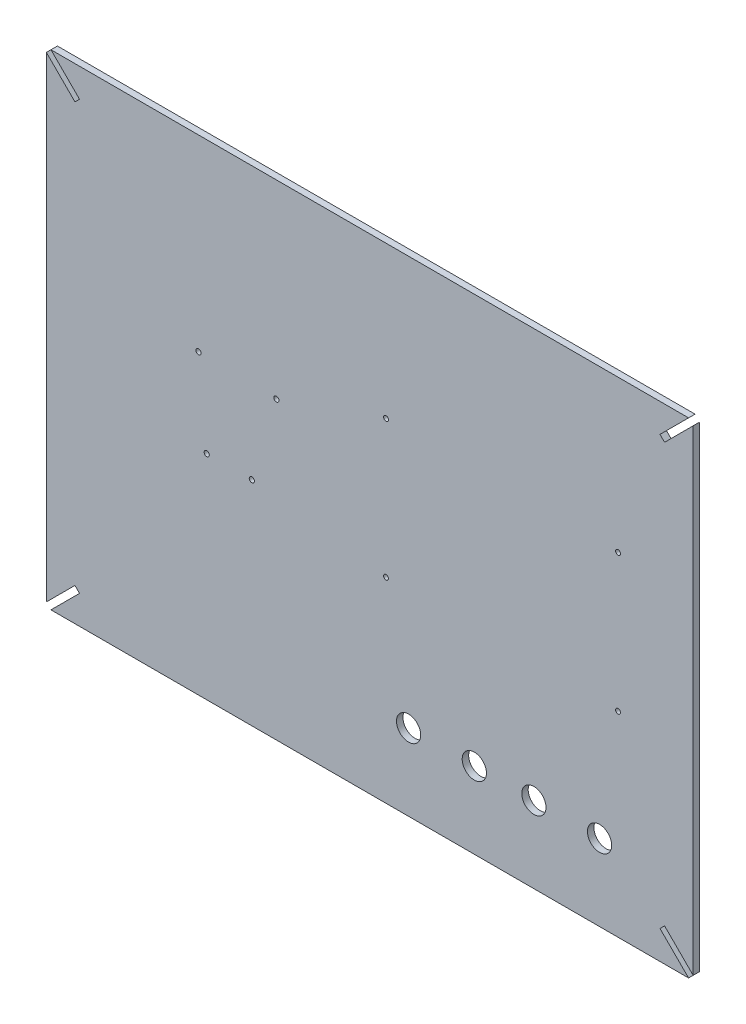
SolidWorks part; units mm, degrees
ref_plane "Plan de face" through (0, 0, 0) normal (0, 0, 1) x (1, 0, 0)
ref_plane "Plan de dessus" through (0, 0, 0) normal (0, 1, 0) x (1, 0, 0)
ref_plane "Plan de droite" through (0, 0, 0) normal (1, 0, 0) x (0, 0, -1)
sketch "Esquisse1" plane through (0, 0, 0) normal (0, 0, 1) x (1, 0, 0)
  line L0 (-443.8564, 119.1502) -> (-49.5132, 119.1502)
  line L1 (-446.6848, 119.1502) -> (-46.6848, 119.1502) construction
  line L2 (-446.6848, 119.1502) -> (-446.6848, -180.8498) construction
  line L3 (-446.6848, -180.8498) -> (-46.6848, -180.8498) construction
  line L4 (-46.6848, 119.1502) -> (-46.6848, -180.8498) construction
  line L5 (-446.6848, 116.3218) -> (-446.6848, -178.0213)
  line L6 (-443.8564, -180.8498) -> (-49.5132, -180.8498)
  line L7 (-46.6848, -178.0213) -> (-46.6848, 116.3218)
  line L8 (-46.6848, 116.3218) -> (-64.3625, 98.6441)
  line L9 (-64.3625, 98.6441) -> (-67.1909, 101.4726)
  line L10 (-67.1909, 101.4726) -> (-49.5132, 119.1502)
  line L11 (-46.6848, -178.0213) -> (-64.3625, -160.3437)
  line L12 (-64.3625, -160.3437) -> (-67.1909, -163.1721)
  line L13 (-67.1909, -163.1721) -> (-49.5132, -180.8498)
  line L14 (-443.8564, -180.8498) -> (-426.1787, -163.1721)
  line L15 (-426.1787, -163.1721) -> (-429.0071, -160.3437)
  line L16 (-429.0071, -160.3437) -> (-446.6848, -178.0213)
  line L17 (-443.8564, 119.1502) -> (-426.1787, 101.4726)
  line L18 (-426.1787, 101.4726) -> (-429.0071, 98.6441)
  line L19 (-429.0071, 98.6441) -> (-446.6848, 116.3218)
  line L20 (-60.4528, -17.2498) -> (-387.6528, -17.2498) construction
  line L21 (-410.2848, 82.7502) -> (-83.0848, 82.7502) construction
  line L22 (-410.2848, 82.7502) -> (-410.2848, -144.4498) construction
  line L23 (-410.2848, -144.4498) -> (-83.0848, -144.4498) construction
  line L24 (-83.0848, 82.7502) -> (-83.0848, -144.4498) construction
  line L25 (-240.4498, 29.1052) -> (-89.3198, 29.1052) construction
  line L26 (-240.4498, 29.1052) -> (-240.4498, -63.6048) construction
  line L27 (-240.4498, -63.6048) -> (-89.3198, -63.6048) construction
  line L28 (-89.3198, 29.1052) -> (-89.3198, -63.6048) construction
  line L29 (-89.3198, 29.1052) -> (-240.4498, -63.6048) construction
  line L30 (-240.4498, 29.1052) -> (-89.3198, -63.6048) construction
  line L31 (-164.8848, 29.1052) -> (-164.8848, -63.6048) construction
  line L32 (-240.4498, -17.2498) -> (-75.4312, -17.2498) construction
  line L33 (-301.8348, -49.0498) -> (-355.1348, -49.0498) construction
  line L34 (-355.1348, 17.0502) -> (-301.8348, 17.0502) construction
  line L35 (-355.1348, 17.0502) -> (-355.1348, -51.5498) construction
  line L36 (-355.1348, -51.5498) -> (-301.8348, -51.5498) construction
  line L37 (-301.8348, 17.0502) -> (-301.8348, -51.5498) construction
  line L38 (-301.8348, 1.7502) -> (-355.1348, 1.7502) construction
  line L39 (-301.8348, 3.0502) -> (-355.1348, 3.0502) construction
  line L40 (-352.6348, 17.0502) -> (-352.6348, -51.5498) construction
  line L41 (-347.5348, 17.0502) -> (-347.5348, -51.5498) construction
  line L42 (-319.6348, 17.0502) -> (-319.6348, -51.5498) construction
  line L43 (-304.4348, 17.0502) -> (-304.4348, -51.5498) construction
  line L44 (-301.8348, -51.5498) -> (-355.1348, 17.0502) construction
  line L45 (-355.1348, 17.0502) -> (-301.8348, 17.0502) construction
  line L46 (-301.8348, 17.0502) -> (-355.1348, -51.5498) construction
  line L47 (-83.0848, -133.6048) -> (-410.2848, -133.6048) construction
  line L48 (-89.3198, -49.0498) -> (-89.3198, -133.6048) construction
  line L49 (-240.4498, -44.0203) -> (-240.4498, -133.6048) construction
  line L50 (-246.6848, -144.4498) -> (-246.6848, 82.7502) construction
  circle A0 centre (-236.6398, 25.2952) radius 1.5
  circle A1 centre (-93.1298, 25.2952) radius 1.5
  circle A2 centre (-236.6398, -59.7948) radius 1.5
  circle A3 centre (-93.1298, -59.7948) radius 1.5
  circle A4 centre (-104.5598, -133.6048) radius 7.5
  circle A5 centre (-347.5348, -49.0498) radius 1.6
  circle A6 centre (-319.6348, -49.0498) radius 1.6
  circle A7 centre (-352.6348, 3.0502) radius 1.6
  circle A8 centre (-304.4348, 1.7502) radius 1.6
  circle A9 centre (-145.1998, -133.6048) radius 7.5
  circle A10 centre (-182.0298, -133.6048) radius 7.5
  circle A11 centre (-222.6698, -133.6048) radius 7.5
  point P30 (-164.8848, -17.2498)
  point P69 (-328.4848, -17.2498)
  dimension "D15" = 3
  dimension "D27" = 3.2
  dimension "D28" = 3.2
  dimension "D29" = 3.2
  dimension "D30" = 3.2
  dimension "D37" = 15
  dimension "D38" = 15
  dimension "D39" = 15
  dimension "D40" = 15
  dimension "D1" = 300
  dimension "D2" = 400
  dimension "D3" = 4
  dimension "D4" = 25
  dimension "D5" = 45
  dimension "D6" = 45
  dimension "D7" = 45
  dimension "D8" = 45
  dimension "D9" = 36.4
  dimension "D10" = 36.4
  dimension "D11" = 36.4
  dimension "D12" = 36.4
  dimension "D13" = 151.13
  dimension "D14" = 92.71
  dimension "D16" = 3.81
  dimension "D17" = 3.81
  dimension "D18" = 27.9
  dimension "D19" = 68.6
  dimension "D20" = 5.1
  dimension "D21" = 2.5
  dimension "D22" = 15.2
  dimension "D23" = 14
  dimension "D24" = 1.3
  dimension "D25" = 50.8
  dimension "D26" = 53.3
  dimension "D31" = 70
  dimension "D32" = 15.24
  dimension "D33" = 40.64
  dimension "D34" = 36.83
  dimension "D35" = 40.64
  dimension "D36" = 17.78
  dimension "D41" = 100
  dimension "D42" = 6.235
  dimension "D43" = 55.15
extrude "Boss.-Extru.1" add sketch "Esquisse1" along normal blind 4
